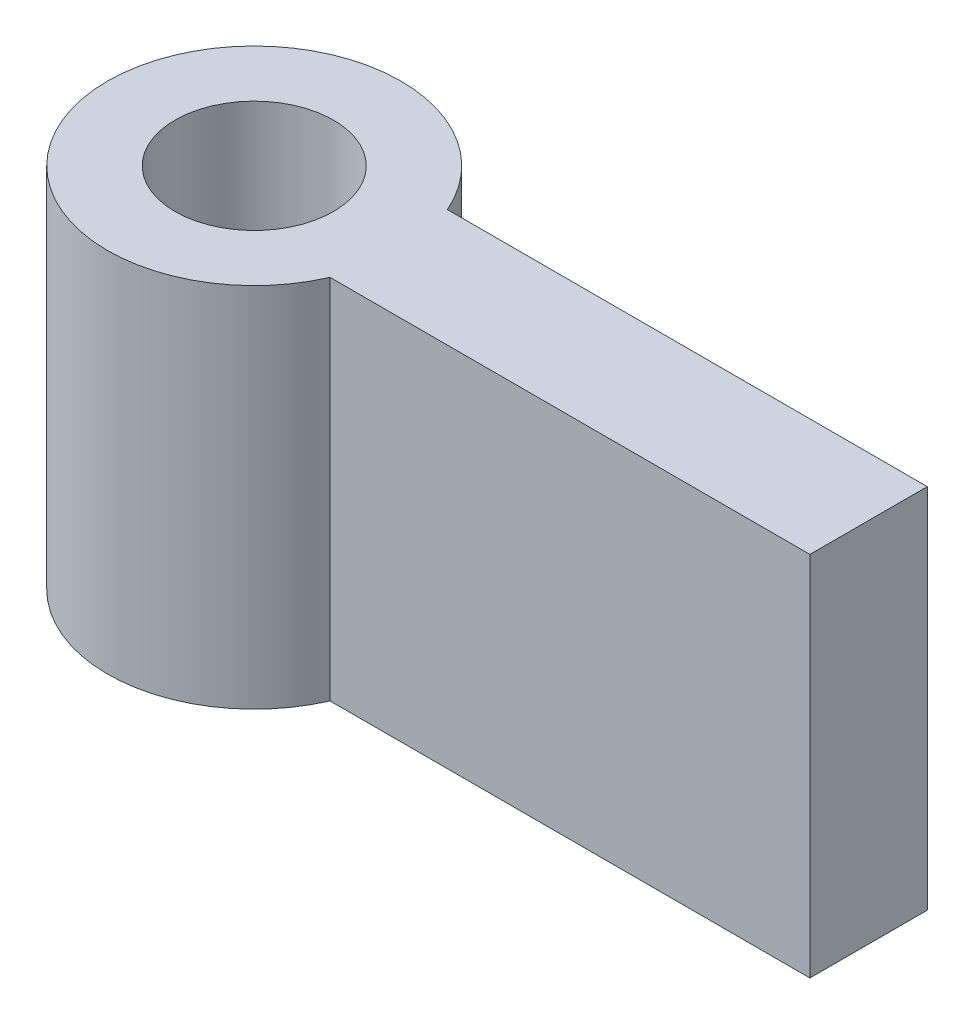
SolidWorks part; units mm, degrees
ref_plane "Front Plane" through (0, 0, 0) normal (0, 0, 1) x (1, 0, 0)
ref_plane "Top Plane" through (0, 0, 0) normal (0, 1, 0) x (1, 0, 0)
ref_plane "Right Plane" through (0, 0, 0) normal (1, 0, 0) x (0, 0, -1)
sketch "Sketch2" plane through (0, 0, 0) normal (0, 1, 0) x (1, 0, 0)
  line L0 (0, 0) -> (20.7658, 0)
  line L1 (20.7658, 0) -> (20.7658, 5.08)
  line L2 (20.7658, 5.08) -> (0, 5.08)
  arc A0 (0, 0) -> (0, 5.08) centre (-5.8199, 2.54) cw
  dimension "D2" = 5.08
extrude "Boss-Extrude1" add sketch "Sketch2" along normal blind 15.875
sketch "Sketch5" plane through (0, 15.875, 0) normal (0, 1, 0) x (1, 0, 0)
  circle A1 centre (-5.8199, 2.54) radius 3.429
extrude "Cut-Extrude1" cut sketch "Sketch5" against normal blind 25.4
